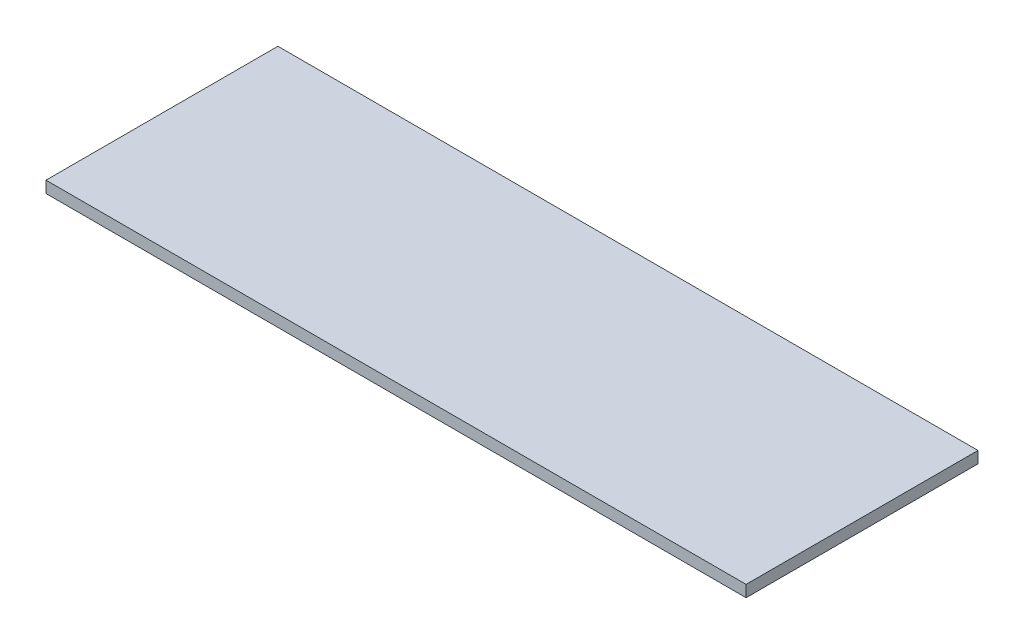
SolidWorks part; units mm, degrees
ref_plane "Front Plane" through (0, 0, 0) normal (0, 0, 1) x (1, 0, 0)
ref_plane "Top Plane" through (0, 0, 0) normal (0, 1, 0) x (1, 0, 0)
ref_plane "Right Plane" through (0, 0, 0) normal (1, 0, 0) x (0, 0, -1)
sketch "Sketch1" plane through (0, 0, 0) normal (0, 1, 0) x (1, 0, 0)
  line L1 (0, 0) -> (1150, 0)
  line L2 (0, 0) -> (0, -380.95)
  line L3 (0, -380.95) -> (1150, -380.95)
  line L4 (1150, 0) -> (1150, -380.95)
  dimension "D1" = 1150
  dimension "D2" = 380.95
extrude "Boss-Extrude1" add sketch "Sketch1" along normal blind 19.05
